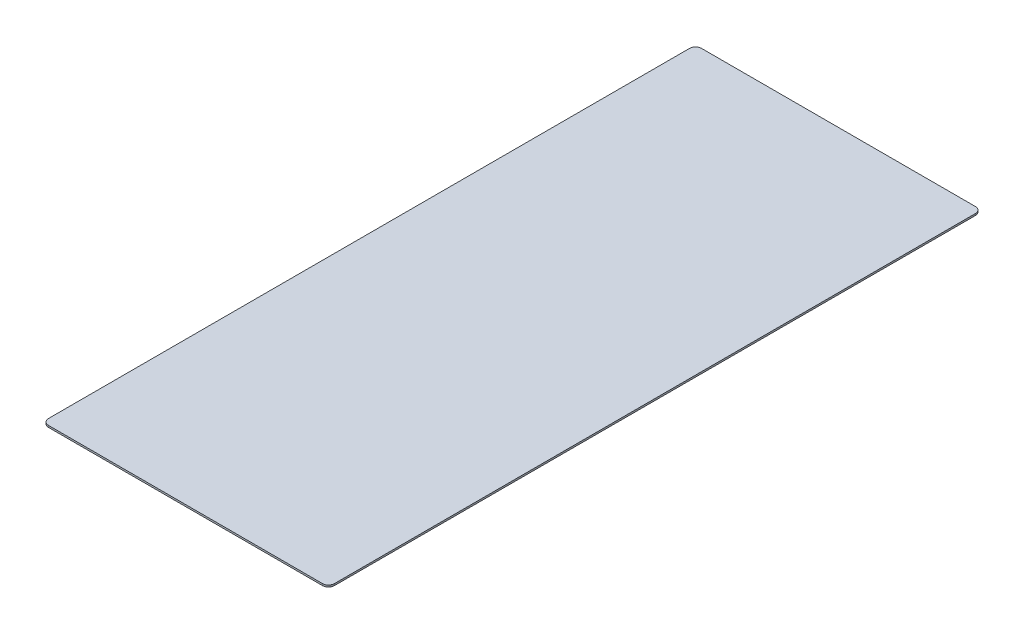
SolidWorks part; units mm, degrees
ref_plane "Front Plane" through (0, 0, 0) normal (0, 0, 1) x (1, 0, 0)
ref_plane "Top Plane" through (0, 0, 0) normal (0, 1, 0) x (1, 0, 0)
ref_plane "Right Plane" through (0, 0, 0) normal (1, 0, 0) x (0, 0, -1)
sketch "Sketch1" plane through (0, 0, 0) normal (0, 1, 0) x (1, 0, 0)
  line L1 (-231.5, -551.5) -> (231.5, -551.5)
  line L2 (-241.5, -541.5) -> (-241.5, 541.5)
  line L3 (-231.5, 551.5) -> (231.5, 551.5)
  line L4 (241.5, -541.5) -> (241.5, 541.5)
  line L5 (-241.5, -551.5) -> (241.5, 551.5) construction
  line L6 (-241.5, 551.5) -> (241.5, -551.5) construction
  arc A0 (231.5, -551.5) -> (241.5, -541.5) centre (231.5, -541.5) ccw
  arc A1 (-231.5, -551.5) -> (-241.5, -541.5) centre (-231.5, -541.5) cw
  arc A2 (-241.5, 541.5) -> (-231.5, 551.5) centre (-231.5, 541.5) cw
  arc A3 (231.5, 551.5) -> (241.5, 541.5) centre (231.5, 541.5) cw
  point P0 (0, 0)
  dimension "D3" = 10
  dimension "D1" = 483
  dimension "D2" = 1103
extrude "Boss-Extrude1" add sketch "Sketch1" along normal blind 3
